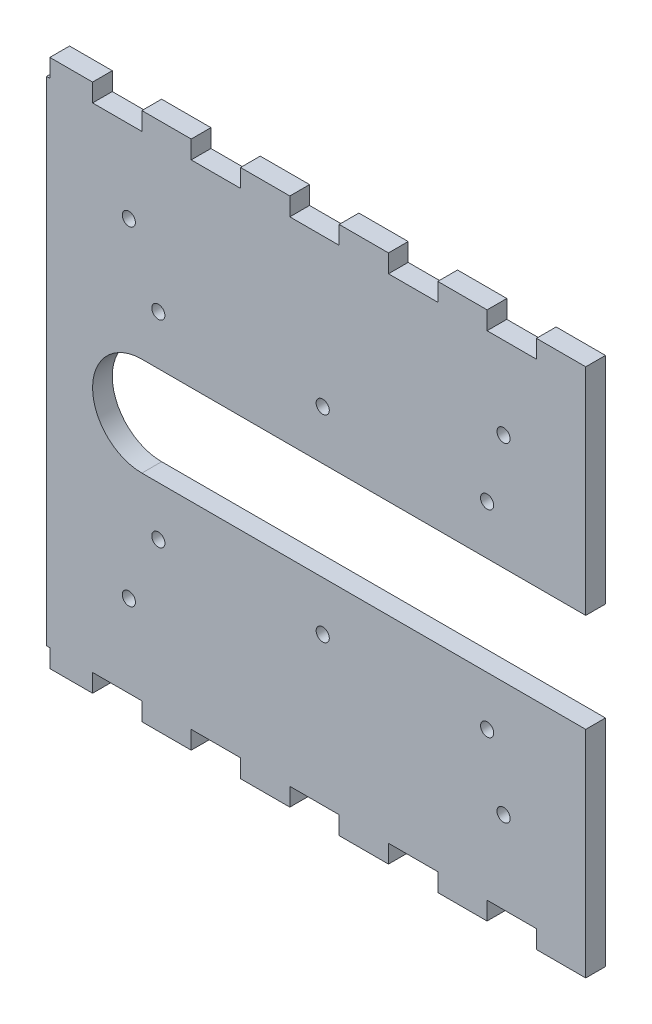
SolidWorks part; units mm, degrees
ref_plane "Front Plane" through (0, 0, 0) normal (0, 0, 1) x (1, 0, 0)
ref_plane "Top Plane" through (0, 0, 0) normal (0, 1, 0) x (1, 0, 0)
ref_plane "Right Plane" through (0, 0, 0) normal (1, 0, 0) x (0, 0, -1)
sketch "Model" plane through (0, 0, 0) normal (0, 0, 1) x (1, 0, 0)
  line L0 (31.3912, 13.6806) -> (46.3912, 13.6806)
  line L1 (61.3912, 13.6806) -> (76.3912, 13.6806)
  line L2 (91.3912, 13.6806) -> (106.3912, 13.6806)
  line L3 (121.3912, 13.6806) -> (136.3912, 13.6806)
  line L4 (151.3912, 13.6806) -> (166.3912, 13.6806)
  line L5 (181.3912, 73.6806) -> (46.3912, 73.6806)
  line L6 (46.3912, 103.6806) -> (181.3912, 103.6806)
  line L7 (166.3912, 163.6806) -> (151.3912, 163.6806)
  line L8 (136.3912, 163.6806) -> (121.3912, 163.6806)
  line L9 (106.3912, 163.6806) -> (91.3912, 163.6806)
  line L10 (76.3912, 163.6806) -> (61.3912, 163.6806)
  line L11 (46.3912, 163.6806) -> (31.3912, 163.6806)
  line L12 (166.3912, 13.6806) -> (166.3912, 8.1806)
  line L13 (151.3912, 13.6806) -> (151.3912, 8.1806)
  line L14 (151.3912, 8.1806) -> (136.3912, 8.1806)
  line L15 (136.3912, 8.1806) -> (136.3912, 13.6806)
  line L16 (166.3912, 8.1806) -> (181.3912, 8.1806)
  line L17 (121.3912, 13.6806) -> (121.3912, 8.1806)
  line L18 (121.3912, 8.1806) -> (106.3912, 8.1806)
  line L19 (106.3912, 8.1806) -> (106.3912, 13.6806)
  line L20 (91.3912, 13.6806) -> (91.3912, 8.1806)
  line L21 (91.3912, 8.1806) -> (76.3912, 8.1806)
  line L22 (76.3912, 8.1806) -> (76.3912, 13.6806)
  line L23 (61.3912, 13.6806) -> (61.3912, 8.1806)
  line L24 (61.3912, 8.1806) -> (46.3912, 8.1806)
  line L25 (46.3912, 8.1806) -> (46.3912, 13.6806)
  line L26 (31.3912, 13.6806) -> (31.3912, 8.1806)
  line L27 (31.3912, 8.1806) -> (18.3912, 8.1806)
  line L28 (166.3912, 163.6806) -> (166.3912, 169.1806)
  line L29 (151.3912, 163.6806) -> (151.3912, 169.1806)
  line L30 (151.3912, 169.1806) -> (136.3912, 169.1806)
  line L31 (136.3912, 169.1806) -> (136.3912, 163.6806)
  line L32 (166.3912, 169.1806) -> (181.3912, 169.1806)
  line L33 (121.3912, 163.6806) -> (121.3912, 169.1806)
  line L34 (121.3912, 169.1806) -> (106.3912, 169.1806)
  line L35 (106.3912, 169.1806) -> (106.3912, 163.6806)
  line L36 (91.3912, 163.6806) -> (91.3912, 169.1806)
  line L37 (91.3912, 169.1806) -> (76.3912, 169.1806)
  line L38 (76.3912, 169.1806) -> (76.3912, 163.6806)
  line L39 (61.3912, 163.6806) -> (61.3912, 169.1806)
  line L40 (61.3912, 169.1806) -> (46.3912, 169.1806)
  line L41 (46.3912, 169.1806) -> (46.3912, 163.6806)
  line L42 (31.3912, 163.6806) -> (31.3912, 169.1806)
  line L43 (31.3912, 169.1806) -> (18.3912, 169.1806)
  line L44 (181.3912, 169.1806) -> (181.3912, 103.6806)
  line L45 (181.3912, 8.1806) -> (181.3912, 73.6806)
  line L46 (18.3912, 169.1806) -> (18.3912, 8.1806)
  circle A0 centre (51.3912, 58.6806) radius 2
  circle A1 centre (101.3912, 58.6806) radius 2
  circle A2 centre (151.3912, 58.6806) radius 2
  circle A3 centre (42.4233, 38.6806) radius 2
  circle A4 centre (156.3912, 38.6806) radius 2
  circle A5 centre (51.3912, 118.6806) radius 2
  circle A6 centre (101.3912, 118.6806) radius 2
  circle A7 centre (151.3912, 118.6806) radius 2
  circle A8 centre (42.4233, 138.6806) radius 2
  circle A9 centre (156.3912, 138.6806) radius 2
  arc A10 (46.3912, 103.6806) -> (46.3912, 73.6806) centre (46.3912, 88.6806) ccw
extrude "Boss-Extrude1" add sketch "Model" along normal blind 6 contours L46 L27 L26 L0 L25 L24 L23 L1 L22 L21 L20 L2 L19 L18 L17 L3 L15 L14 L13 L4 L12 L16 L45 L5 A10 L6 L44 L32 L28 L7 L29 L30 L31 L8 L33 L34 L35 L9 L36 L37 L38 L10 L39 L40 L41 L11 L42 L43 | A8 | A5 | A6 | A9 | A7 | A2 | A4 | A1 | A0 | A3
sketch "Sketch2" plane through (18.3912, 0, 0) normal (-1, 0, 0) x (0, 0, 1)
  line L0 (0, 169.1806) -> (6, 8.1806) construction
  line L1 (6, 169.1806) -> (6, 8.1806) construction
  line L2 (0, 163.6806) -> (6, 163.6806)
  line L3 (0, 163.6806) -> (0, 13.6806)
  line L4 (0, 13.6806) -> (6, 13.6806)
  line L5 (6, 163.6806) -> (6, 13.6806)
  line L6 (0, 163.6806) -> (6, 13.6806) construction
  line L7 (0, 13.6806) -> (6, 163.6806) construction
  line L8 (6, 169.1806) -> (0, 169.1806) construction
  point P4 (3, 88.6806)
  dimension "D1" = 5.5
extrude "Boss-Extrude2" add sketch "Sketch2" along normal blind 1
